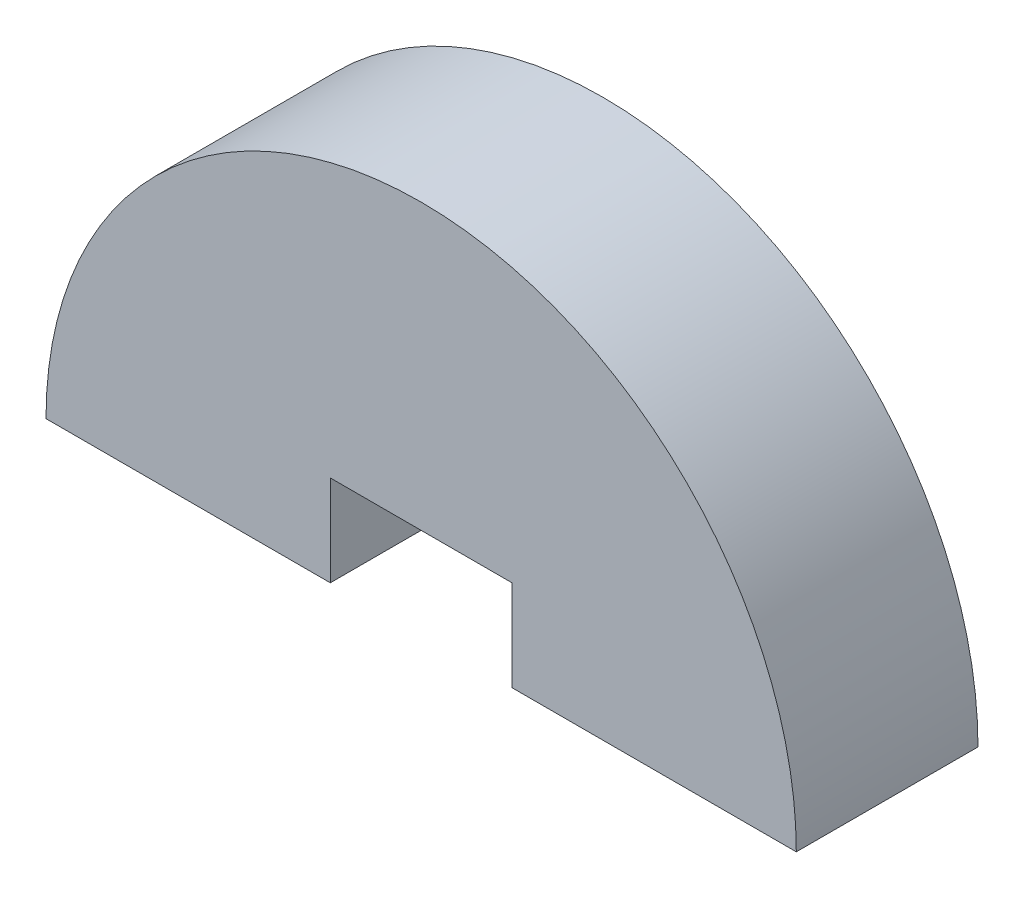
SolidWorks part; units mm, degrees
ref_plane "Front Plane" through (0, 0, 0) normal (0, 0, 1) x (1, 0, 0)
ref_plane "Top Plane" through (0, 0, 0) normal (0, 1, 0) x (1, 0, 0)
ref_plane "Right Plane" through (0, 0, 0) normal (1, 0, 0) x (0, 0, -1)
sketch "Model" plane through (0, 0, 0) normal (0, 0, 1) x (1, 0, 0)
  line L0 (3761.8088, 1712.0899) -> (3771.1973, 1712.0899)
  line L1 (3777.1973, 1712.0899) -> (3786.5858, 1712.0899)
  line L2 (3777.1973, 1712.0899) -> (3777.1973, 1715.0899)
  line L3 (3777.1973, 1715.0899) -> (3771.1973, 1715.0899)
  line L4 (3771.1973, 1715.0899) -> (3771.1973, 1712.0899)
  arc A0 (3786.5858, 1712.0899) -> (3761.8088, 1712.0899) centre (3774.1973, 1712.0899) ccw
extrude "Boss-Extrude1" add sketch "Model" along normal blind 6 contours A0 L0 L4 L3 L2 L1
